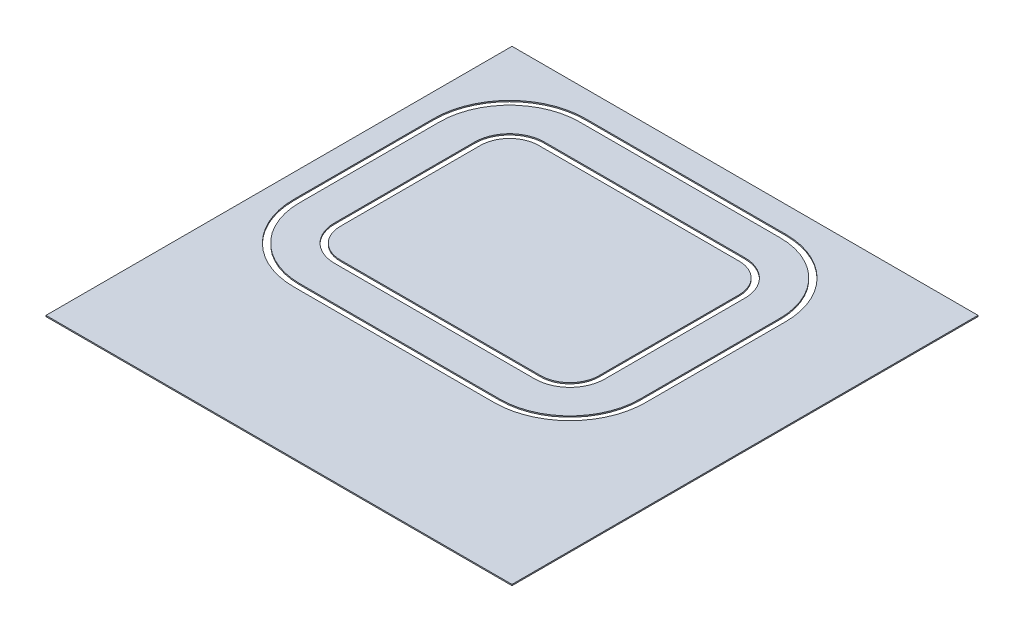
SolidWorks part; units mm, degrees
ref_plane "Front Plane" through (0, 0, 0) normal (0, 0, 1) x (1, 0, 0)
ref_plane "Top Plane" through (0, 0, 0) normal (0, 1, 0) x (1, 0, 0)
ref_plane "Right Plane" through (0, 0, 0) normal (1, 0, 0) x (0, 0, -1)
sketch "Sketch1" plane through (0, 0, 0) normal (0, 1, 0) x (1, 0, 0)
  line L1 (-2000, 2000) -> (2000, 2000)
  line L2 (-2000, 2000) -> (-2000, -2000)
  line L3 (-2000, -2000) -> (2000, -2000)
  line L4 (2000, 2000) -> (2000, -2000)
  line L5 (-1148.6969, 1427.6606) -> (571.8195, 1427.6606)
  line L6 (-1448.6969, 1127.6606) -> (-1448.6969, -74.9801)
  line L7 (-1148.6969, -374.9801) -> (571.8195, -374.9801)
  line L8 (871.8195, 1127.6606) -> (871.8195, -74.9801)
  line L9 (-1148.6969, 1377.6606) -> (571.8195, 1377.6606)
  line L10 (-1398.6969, 1127.6606) -> (-1398.6969, -74.9801)
  line L11 (-1148.6969, -324.9801) -> (571.8195, -324.9801)
  line L12 (821.8195, 1127.6606) -> (821.8195, -74.9801)
  line L13 (-1148.6969, 1727.6606) -> (571.8195, 1727.6606)
  line L14 (-1748.6969, 1127.6606) -> (-1748.6969, -74.9801)
  line L15 (-1148.6969, -674.9801) -> (571.8195, -674.9801)
  line L16 (1171.8195, 1127.6606) -> (1171.8195, -74.9801)
  line L17 (-1148.6969, 1777.6606) -> (571.8195, 1777.6606)
  line L18 (-1798.6969, 1127.6606) -> (-1798.6969, -74.9801)
  line L19 (-1148.6969, -724.9801) -> (571.8195, -724.9801)
  line L20 (1221.8195, 1127.6606) -> (1221.8195, -74.9801)
  arc A0 (571.8195, 1427.6606) -> (871.8195, 1127.6606) centre (571.8195, 1127.6606) cw
  arc A1 (571.8195, -374.9801) -> (871.8195, -74.9801) centre (571.8195, -74.9801) ccw
  arc A2 (-1448.6969, -74.9801) -> (-1148.6969, -374.9801) centre (-1148.6969, -74.9801) ccw
  arc A3 (-1148.6969, 1427.6606) -> (-1448.6969, 1127.6606) centre (-1148.6969, 1127.6606) ccw
  arc A4 (571.8195, -324.9801) -> (821.8195, -74.9801) centre (571.8195, -74.9801) ccw
  arc A5 (571.8195, 1377.6606) -> (821.8195, 1127.6606) centre (571.8195, 1127.6606) cw
  arc A6 (-1398.6969, -74.9801) -> (-1148.6969, -324.9801) centre (-1148.6969, -74.9801) ccw
  arc A7 (-1148.6969, 1377.6606) -> (-1398.6969, 1127.6606) centre (-1148.6969, 1127.6606) ccw
  arc A8 (571.8195, 1727.6606) -> (1171.8195, 1127.6606) centre (571.8195, 1127.6606) cw
  arc A9 (571.8195, -674.9801) -> (1171.8195, -74.9801) centre (571.8195, -74.9801) ccw
  arc A10 (-1748.6969, -74.9801) -> (-1148.6969, -674.9801) centre (-1148.6969, -74.9801) ccw
  arc A11 (-1148.6969, 1727.6606) -> (-1748.6969, 1127.6606) centre (-1148.6969, 1127.6606) ccw
  arc A12 (571.8195, -724.9801) -> (1221.8195, -74.9801) centre (571.8195, -74.9801) ccw
  arc A13 (571.8195, 1777.6606) -> (1221.8195, 1127.6606) centre (571.8195, 1127.6606) cw
  arc A14 (-1148.6969, 1777.6606) -> (-1798.6969, 1127.6606) centre (-1148.6969, 1127.6606) ccw
  arc A15 (-1798.6969, -74.9801) -> (-1148.6969, -724.9801) centre (-1148.6969, -74.9801) ccw
  point P4 (0, 2000)
  point P6 (-2000, 0)
  dimension "D3" = 300
  dimension "D8" = 250
  dimension "D13" = 600
  dimension "D19" = 650
  dimension "D1" = 4000
  dimension "D2" = 4000
  dimension "D4" = 50
  dimension "D5" = 50
  dimension "D6" = 50
  dimension "D7" = 50
  dimension "D9" = 300
  dimension "D10" = 300
  dimension "D11" = 300
  dimension "D12" = 300
  dimension "D14" = 50
  dimension "D16" = 50
  dimension "D17" = 50
  dimension "D18" = 50
extrude "Boss-Extrude2" add sketch "Sketch1" along normal blind 10 contours L4 L1 L2 L3 A15 L18 A14 L17 A13 L20 A12 L19 | L13 A11 L14 A10 L15 A9 L16 A8 A3 L5 A0 L8 A1 L7 A2 L6 | L9 A7 L10 A6 L11 A4 L12 A5
